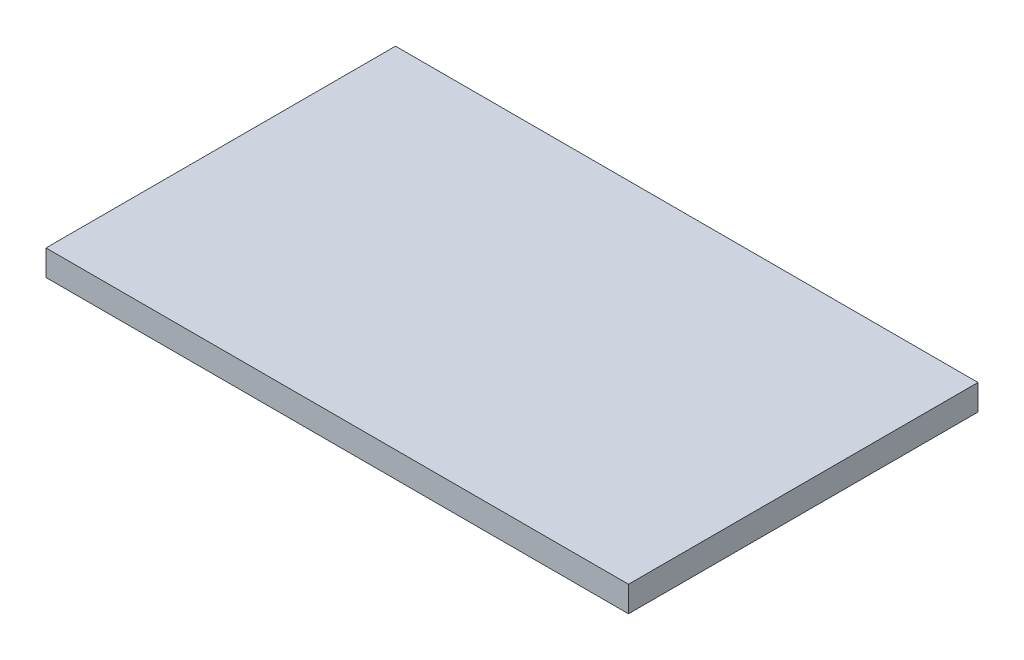
SolidWorks part; units mm, degrees
ref_plane "Front Plane" through (0, 0, 0) normal (0, 0, 1) x (1, 0, 0)
ref_plane "Top Plane" through (0, 0, 0) normal (0, 1, 0) x (1, 0, 0)
ref_plane "Right Plane" through (0, 0, 0) normal (1, 0, 0) x (0, 0, -1)
sketch "Sketch1" plane through (0, 0, 0) normal (0, 1, 0) x (1, 0, 0)
  line L1 (0, 0) -> (125, 0)
  line L2 (0, 0) -> (0, 75)
  line L3 (0, 75) -> (125, 75)
  line L4 (125, 0) -> (125, 75)
extrude "Boss-Extrude2" add sketch "Sketch1" along normal blind 5.5
